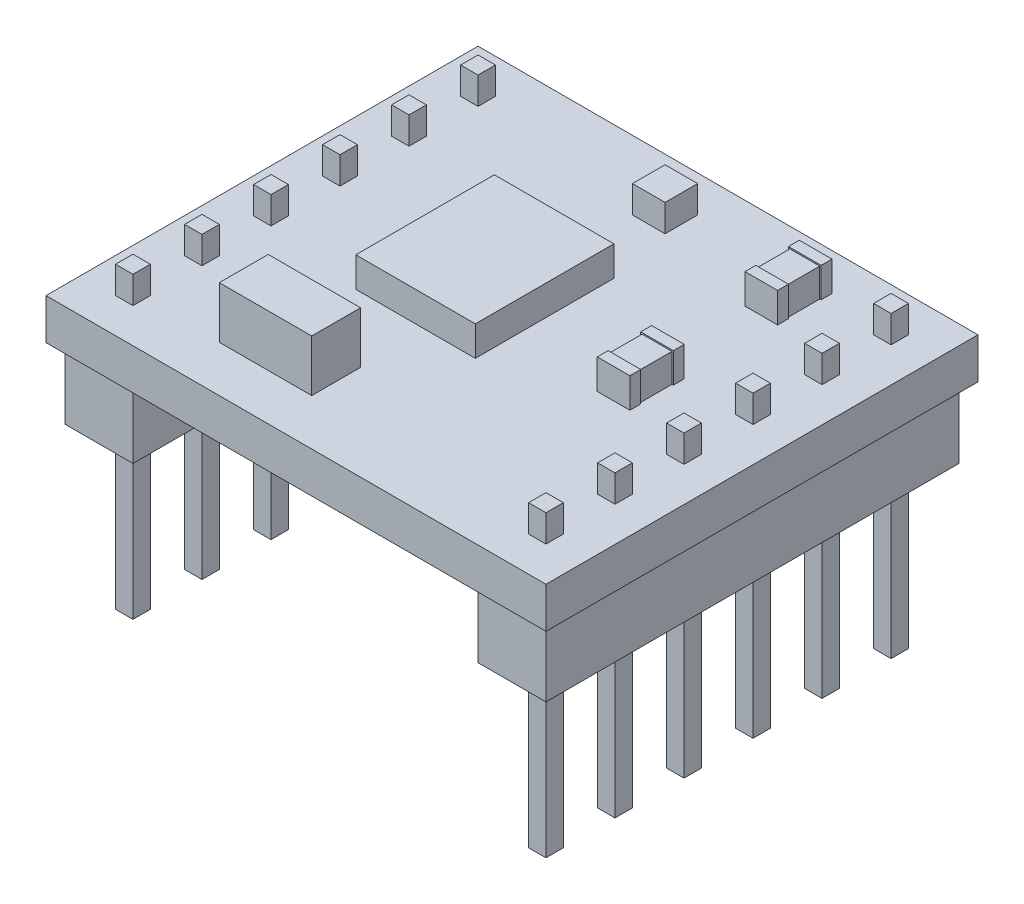
SolidWorks part; units mm, degrees
ref_plane "Front Plane" through (0, 0, 0) normal (0, 0, 1) x (1, 0, 0)
ref_plane "Top Plane" through (0, 0, 0) normal (0, 1, 0) x (1, 0, 0)
ref_plane "Right Plane" through (0, 0, 0) normal (1, 0, 0) x (0, 0, -1)
sketch "Sketch1" plane through (0, 0, 0) normal (0, 1, 0) x (1, 0, 0)
  line L0 (-9.2, 7.95) -> (9.2, -7.95) construction
  line L1 (-9.2, 7.95) -> (9.2, 7.95)
  line L2 (-9.2, 7.95) -> (-9.2, -7.95)
  line L3 (-9.2, -7.95) -> (9.2, -7.95)
  line L4 (9.2, 7.95) -> (9.2, -7.95)
  point P5 (0, 0)
  point P6 (0, 0)
  point P7 (0, 0)
  dimension "D1" = 18.4
  dimension "D2" = 15.9
extrude "Boss-Extrude1" add sketch "Sketch1" against normal blind 1.5
sketch "Sketch2" plane through (0, -1.5, 0) normal (0, -1, 0) x (1, 0, 0)
  line L0 (9.2, -7.95) -> (-9.2, -7.95) construction
  line L1 (-8.85, 7.6) -> (-6.35, 7.6)
  line L2 (-8.85, 7.6) -> (-8.85, -7.6)
  line L3 (-8.85, -7.6) -> (-6.35, -7.6)
  line L4 (-6.35, 7.6) -> (-6.35, -7.6)
  line L9 (-9.2, 7.95) -> (9.2, 7.95) construction
  line L10 (-9.2, -7.95) -> (-9.2, 7.95) construction
  dimension "D1" = 2.5
  dimension "D2" = 0.35
  dimension "D3" = 0.35
  dimension "D4" = 0.35
extrude "Boss-Extrude2" add sketch "Sketch2" along normal blind 2.6
sketch "Sketch3" plane through (0, -4.1, 0) normal (0, -1, 0) x (-1, 0, 0)
  line L0 (6.35, -7.6) -> (8.85, -7.6) construction
  line L1 (7.92, -6.03) -> (7.28, -6.03)
  line L2 (7.92, -6.03) -> (7.92, -6.67)
  line L3 (7.92, -6.67) -> (7.28, -6.67)
  line L4 (7.28, -6.03) -> (7.28, -6.67)
  line L5 (7.92, -6.03) -> (7.28, -6.67) construction
  line L6 (7.92, -6.67) -> (7.28, -6.03) construction
  line L7 (7.92, -3.49) -> (7.28, -3.49)
  line L8 (7.92, -3.49) -> (7.92, -4.13)
  line L9 (7.92, -4.13) -> (7.28, -4.13)
  line L10 (7.28, -3.49) -> (7.28, -4.13)
  line L11 (7.92, -3.49) -> (7.28, -4.13) construction
  line L12 (7.92, -4.13) -> (7.28, -3.49) construction
  line L13 (7.92, -0.95) -> (7.28, -0.95)
  line L14 (7.92, -0.95) -> (7.92, -1.59)
  line L15 (7.92, -1.59) -> (7.28, -1.59)
  line L16 (7.28, -0.95) -> (7.28, -1.59)
  line L17 (7.92, -0.95) -> (7.28, -1.59) construction
  line L18 (7.92, -1.59) -> (7.28, -0.95) construction
  line L25 (7.92, 1.59) -> (7.28, 1.59)
  line L26 (7.92, 1.59) -> (7.92, 0.95)
  line L27 (7.92, 0.95) -> (7.28, 0.95)
  line L28 (7.28, 1.59) -> (7.28, 0.95)
  line L29 (7.92, 1.59) -> (7.28, 0.95) construction
  line L30 (7.92, 0.95) -> (7.28, 1.59) construction
  line L31 (7.92, 6.67) -> (7.28, 6.67)
  line L32 (7.92, 6.67) -> (7.92, 6.03)
  line L33 (7.92, 6.03) -> (7.28, 6.03)
  line L34 (7.28, 6.67) -> (7.28, 6.03)
  line L35 (7.92, 6.67) -> (7.28, 6.03) construction
  line L36 (7.92, 6.03) -> (7.28, 6.67) construction
  line L37 (7.92, 4.13) -> (7.28, 4.13)
  line L38 (7.92, 4.13) -> (7.92, 3.49)
  line L39 (7.92, 3.49) -> (7.28, 3.49)
  line L40 (7.28, 4.13) -> (7.28, 3.49)
  line L41 (7.92, 4.13) -> (7.28, 3.49) construction
  line L42 (7.92, 3.49) -> (7.28, 4.13) construction
  line L43 (7.6, -0.95) -> (7.6, 0.95) construction
  line L44 (8.85, -7.6) -> (8.85, 7.6) construction
  point P0 (7.6, -6.35)
  point P8 (7.6, -7.6)
  point P9 (7.6, -3.81)
  point P14 (7.6, -1.27)
  point P20 (8.85, 0)
  point P21 (7.6, 0)
  point P24 (7.6, 1.27)
  point P29 (7.6, 6.35)
  point P34 (7.6, 3.81)
  dimension "D1" = 2.54
  dimension "D2" = 2.54
  dimension "D3" = 2.54
  dimension "D4" = 2.54
  dimension "D5" = 2.54
  dimension "D6" = 0.64
extrude "Boss-Extrude3" add sketch "Sketch3" along normal blind 5.9 and the other way blind 5.1
mirror "Mirror1" about plane through (0, 0, 0) normal (1, 0, 0) of "Boss-Extrude2", "Boss-Extrude3"
sketch "Sketch5" plane through (0, 0, 0) normal (0, 1, 0) x (1, 0, 0)
  line L0 (9.2, 7.95) -> (-9.2, 7.95) construction
  line L5 (-3.7, 3.05) -> (0.7, 3.05)
  line L6 (-3.7, 3.05) -> (-3.7, -2.05)
  line L7 (-3.7, -2.05) -> (0.7, -2.05)
  line L8 (0.7, 3.05) -> (0.7, -2.05)
  line L13 (3.9979, 1.1395) -> (5.1979, 1.1395)
  line L14 (3.9979, 1.1395) -> (3.9979, -0.8605)
  line L15 (3.9979, -0.8605) -> (5.1979, -0.8605)
  line L16 (5.1979, 1.1395) -> (5.1979, -0.8605)
  line L17 (3.9979, 6.5766) -> (5.1979, 6.5766)
  line L18 (3.9979, 6.5766) -> (3.9979, 4.5766)
  line L19 (3.9979, 4.5766) -> (5.1979, 4.5766)
  line L20 (5.1979, 6.5766) -> (5.1979, 4.5766)
  line L21 (-9.2, 7.95) -> (-9.2, -7.95) construction
  dimension "D1" = 1.2
  dimension "D2" = 2
  dimension "D3" = 2
  dimension "D4" = 4.4
  dimension "D5" = 5.1
  dimension "D6" = 4.9
  dimension "D7" = 5.5
  dimension "D8" = 3.2979
  dimension "D9" = 3.4371
  dimension "D10" = 1.1895
extrude "Boss-Extrude4" add sketch "Sketch5" along normal blind 1.1
sketch "Sketch6" plane through (0, 0, 0) normal (0, 1, 0) x (1, 0, 0)
  line L0 (0.7, 3.05) -> (-3.7, 3.05) construction
  line L1 (-0.9788, 6.6122) -> (0.2212, 6.6122)
  line L2 (-0.9788, 6.6122) -> (-0.9788, 5.4122)
  line L3 (-0.9788, 5.4122) -> (0.2212, 5.4122)
  line L4 (0.2212, 6.6122) -> (0.2212, 5.4122)
  line L5 (3.9979, 6.5766) -> (3.9979, 4.5766) construction
  dimension "D1" = 1.2
  dimension "D2" = 1.2
  dimension "D3" = 2.3622
  dimension "D4" = 3.7767
extrude "Boss-Extrude5" add sketch "Sketch6" along normal blind 1
sketch "Sketch7" plane through (0, 0, 0) normal (0, 1, 0) x (1, 0, 0)
  line L0 (-3.7, -2.05) -> (0.7, -2.05) construction
  line L1 (-4.5238, -4.4484) -> (-1.1238, -4.4484)
  line L2 (-4.5238, -4.4484) -> (-4.5238, -6.2484)
  line L3 (-4.5238, -6.2484) -> (-1.1238, -6.2484)
  line L4 (-1.1238, -4.4484) -> (-1.1238, -6.2484)
  line L5 (-3.7, 3.05) -> (-3.7, -2.05) construction
  point P4 (-2.8238, -4.4484)
  dimension "D1" = 3.4
  dimension "D2" = 1.8
  dimension "D3" = 2.3984
  dimension "D4" = 0.8238
extrude "Boss-Extrude6" add sketch "Sketch7" along normal blind 1.9
sketch "Sketch8" plane through (0, 1.1, 0) normal (0, 1, 0) x (1, 0, 0)
  line L0 (3.9979, 6.5766) -> (3.9979, 4.5766) construction
  line L1 (3.9979, 6.1766) -> (5.1979, 6.1766)
  line L2 (3.9979, 6.1766) -> (3.9979, 4.9766)
  line L3 (3.9979, 4.9766) -> (5.1979, 4.9766)
  line L4 (5.1979, 6.1766) -> (5.1979, 4.9766)
  line L5 (5.1979, 4.5766) -> (5.1979, 6.5766) construction
  line L6 (3.9979, 1.1395) -> (3.9979, -0.8605) construction
  line L7 (3.9979, 0.7395) -> (5.1979, 0.7395)
  line L8 (3.9979, 0.7395) -> (3.9979, -0.4605)
  line L9 (3.9979, -0.4605) -> (5.1979, -0.4605)
  line L10 (5.1979, 0.7395) -> (5.1979, -0.4605)
  line L11 (5.1979, -0.8605) -> (5.1979, 1.1395) construction
  line L13 (5.1979, 1.1395) -> (3.9979, 1.1395) construction
  line L14 (5.1979, 6.5766) -> (3.9979, 6.5766) construction
  dimension "D1" = 1.2
  dimension "D2" = 1.2
  dimension "D3" = 0.4
  dimension "D4" = 0.4
extrude "Cut-Extrude1" cut sketch "Sketch8" against normal blind 0.05
sketch "Sketch9" plane through (3.9979, 0, 0) normal (-1, 0, 0) x (0, 0, 1)
  line L0 (-1.1395, 0) -> (0.8605, 0) construction
  line L1 (-0.7395, 1.05) -> (0.4605, 1.05)
  line L2 (-0.7395, 1.05) -> (-0.7395, 0)
  line L3 (-0.7395, 0) -> (0.4605, 0)
  line L4 (0.4605, 1.05) -> (0.4605, 0)
  line L5 (-6.5766, 0) -> (-4.5766, 0) construction
  line L6 (-6.1766, 1.05) -> (-4.9766, 1.05)
  line L7 (-6.1766, 1.05) -> (-6.1766, 0)
  line L8 (-6.1766, 0) -> (-4.9766, 0)
  line L9 (-4.9766, 1.05) -> (-4.9766, 0)
extrude "Cut-Extrude2" cut sketch "Sketch9" against normal blind 0.05
sketch "Sketch10" plane through (5.1979, 0, 0) normal (1, 0, 0) x (0, 0, -1)
  line L0 (-0.8605, 0) -> (1.1395, 0) construction
  line L1 (-0.4605, 1.05) -> (0.7395, 1.05)
  line L2 (-0.4605, 1.05) -> (-0.4605, 0)
  line L3 (-0.4605, 0) -> (0.7395, 0)
  line L4 (0.7395, 1.05) -> (0.7395, 0)
  line L5 (-7.95, 0) -> (7.95, 0) construction
  line L6 (6.1766, 1.05) -> (4.9766, 1.05)
  line L7 (6.1766, 1.05) -> (6.1766, 0)
  line L8 (6.1766, 0) -> (4.9766, 0)
  line L9 (4.9766, 1.05) -> (4.9766, 0)
  dimension "D1" = 1.2
  dimension "D2" = 1.2
extrude "Cut-Extrude3" cut sketch "Sketch10" against normal blind 0.05
